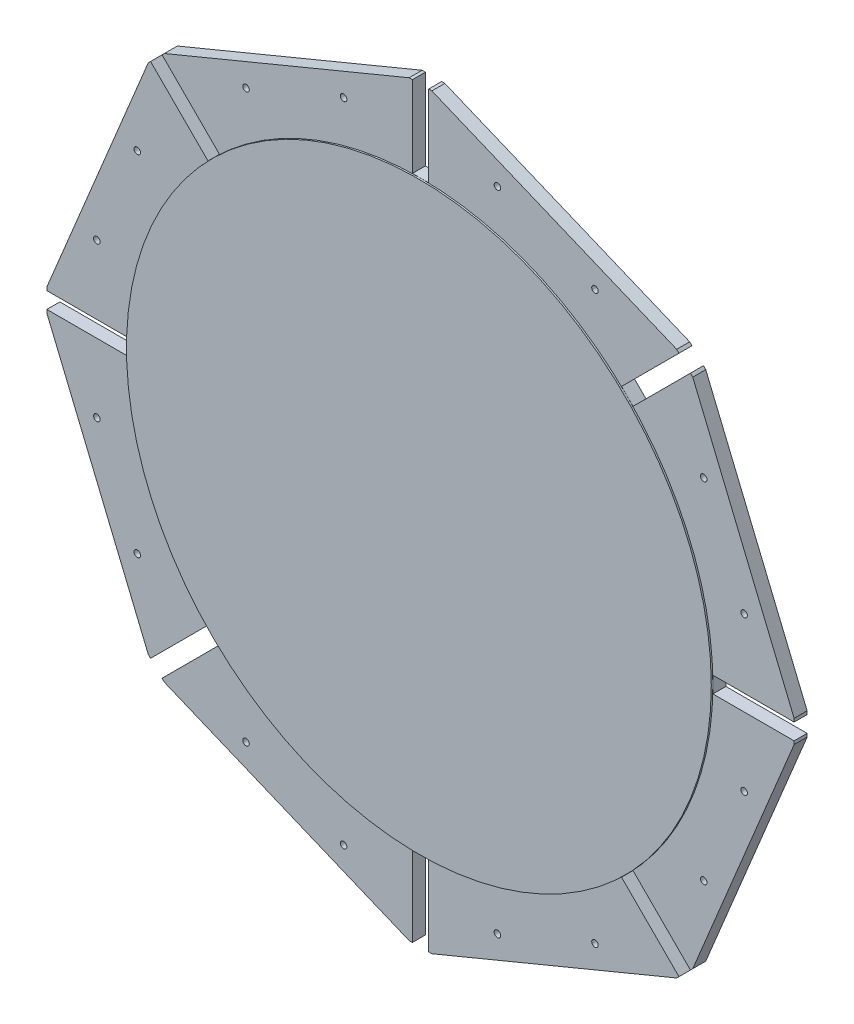
SolidWorks part; units mm, degrees
ref_plane "Front Plane" through (0, 0, 0) normal (0, 0, 1) x (1, 0, 0)
ref_plane "Top Plane" through (0, 0, 0) normal (0, 1, 0) x (1, 0, 0)
ref_plane "Right Plane" through (0, 0, 0) normal (1, 0, 0) x (0, 0, -1)
sketch "Sketch1" plane through (0, 0, 0) normal (0, 0, 1) x (1, 0, 0)
  line L0 (5, 230) -> (5, 180)
  line L1 (5, 180) -> (-5, 180)
  line L2 (-5, 180) -> (-5, 230)
  line L3 (-5, 230) -> (-7, 230)
  line L4 (-7, 230) -> (-157.6848, 167.5843)
  line L5 (-157.6848, 167.5843) -> (-159.099, 166.1701)
  line L6 (-159.099, 166.1701) -> (-123.7437, 130.8148)
  line L7 (-123.7437, 130.8148) -> (-130.8148, 123.7437)
  line L8 (-130.8148, 123.7437) -> (-166.1701, 159.099)
  line L9 (-166.1701, 159.099) -> (-167.5843, 157.6848)
  line L10 (-167.5843, 157.6848) -> (-230, 7)
  line L11 (-230, 7) -> (-230, 5)
  line L12 (-230, 5) -> (-180, 5)
  line L13 (-180, 5) -> (-180, -5)
  line L14 (-180, -5) -> (-230, -5)
  line L15 (-230, -5) -> (-230, -7)
  line L16 (-230, -7) -> (-167.5843, -157.6848)
  line L17 (-167.5843, -157.6848) -> (-166.1701, -159.099)
  line L18 (-166.1701, -159.099) -> (-130.8148, -123.7437)
  line L19 (-130.8148, -123.7437) -> (-123.7437, -130.8148)
  line L20 (-123.7437, -130.8148) -> (-159.099, -166.1701)
  line L21 (-159.099, -166.1701) -> (-157.6848, -167.5843)
  line L22 (-157.6848, -167.5843) -> (-7, -230)
  line L23 (-7, -230) -> (-5, -230)
  line L24 (-5, -230) -> (-5, -180)
  line L25 (-5, -180) -> (5, -180)
  line L26 (5, -180) -> (5, -230)
  line L27 (5, -230) -> (7, -230)
  line L28 (7, -230) -> (157.6848, -167.5843)
  line L29 (157.6848, -167.5843) -> (159.099, -166.1701)
  line L30 (159.099, -166.1701) -> (123.7437, -130.8148)
  line L31 (123.7437, -130.8148) -> (130.8148, -123.7437)
  line L32 (130.8148, -123.7437) -> (166.1701, -159.099)
  line L33 (166.1701, -159.099) -> (167.5843, -157.6848)
  line L34 (167.5843, -157.6848) -> (230, -7)
  line L35 (230, -7) -> (230, -5)
  line L36 (230, -5) -> (180, -5)
  line L37 (180, -5) -> (180, 5)
  line L38 (180, 5) -> (230, 5)
  line L39 (230, 5) -> (230, 7)
  line L40 (230, 7) -> (167.5843, 157.6848)
  line L41 (167.5843, 157.6848) -> (166.1701, 159.099)
  line L42 (166.1701, 159.099) -> (130.8148, 123.7437)
  line L43 (130.8148, 123.7437) -> (123.7437, 130.8148)
  line L44 (123.7437, 130.8148) -> (159.099, 166.1701)
  line L45 (159.099, 166.1701) -> (157.6848, 167.5843)
  line L46 (157.6848, 167.5843) -> (7, 230)
  line L47 (7, 230) -> (5, 230)
  line L48 (0, 180) -> (0, -180) construction
  line L49 (-180, 0) -> (180, 0) construction
  dimension "D1" = 163.1001
  dimension "D2" = 10
extrude "Boss-Extrude1" add sketch "Sketch1" along normal blind 8
sketch "Sketch2" plane through (0, 0, 8) normal (0, 0, 1) x (1, 0, 0)
  line L0 (5, 180) -> (-5, 180) construction
  circle A0 centre (0, 0) radius 180
  point P0 (0, 180)
extrude "Boss-Extrude2" add sketch "Sketch2" along normal blind 1
sketch "Sketch3" plane through (0, 0, 8) normal (0, 0, 1) x (1, 0, 0)
  circle A0 centre (107.3978, 174.3545) radius 2
  circle A1 centre (47.3456, 199.2289) radius 2
  circle A3 centre (199.2289, 47.3456) radius 2
  circle A4 centre (174.3545, 107.3978) radius 2
  circle A5 centre (174.3545, -107.3978) radius 2
  circle A6 centre (199.2289, -47.3456) radius 2
  circle A7 centre (47.3456, -199.2289) radius 2
  circle A8 centre (107.3978, -174.3545) radius 2
  circle A9 centre (-107.3978, -174.3545) radius 2
  circle A10 centre (-47.3456, -199.2289) radius 2
  circle A11 centre (-199.2289, -47.3456) radius 2
  circle A12 centre (-174.3545, -107.3978) radius 2
  circle A13 centre (-174.3545, 107.3978) radius 2
  circle A14 centre (-199.2289, 47.3456) radius 2
  circle A15 centre (-47.3456, 199.2289) radius 2
  circle A16 centre (-107.3978, 174.3545) radius 2
  point P37 (0, 0)
  dimension "D1" = 8
extrude "Cut-Extrude1" cut sketch "Sketch3" against normal up to next
sketch "Sketch4" plane through (0, 0, 0) normal (0, 0, -1) x (-1, 0, 0)
  circle A0 centre (-0.5579, 0.279) radius 45
  dimension "D1" = 90
